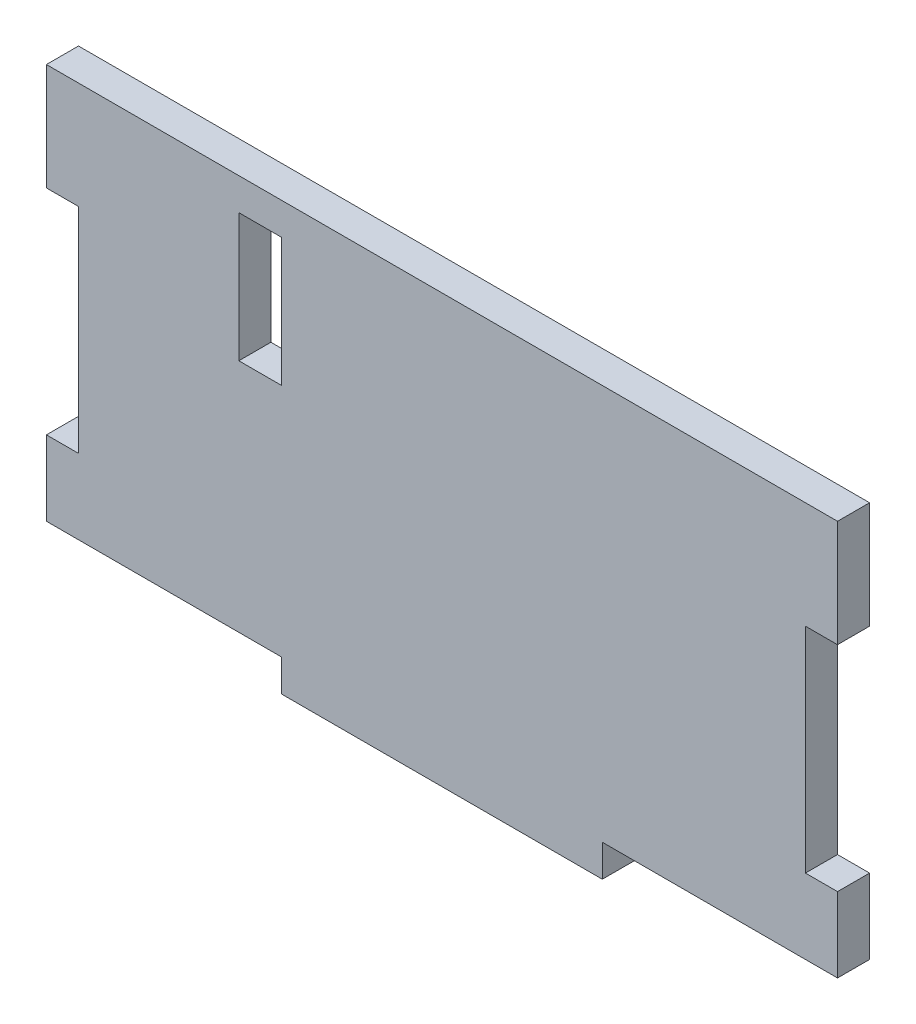
SolidWorks part; units mm, degrees
ref_plane "Plano frontal" through (0, 0, 0) normal (0, 0, 1) x (1, 0, 0)
ref_plane "Plano superior" through (0, 0, 0) normal (0, 1, 0) x (1, 0, 0)
ref_plane "Plano direito" through (0, 0, 0) normal (1, 0, 0) x (0, 0, -1)
sketch "Esboço1" plane through (0, 0, 0) normal (0, 0, 1) x (1, 0, 0)
  line L1 (-37, -20) -> (37, -20)
  line L2 (-37, -20) -> (-37, 20)
  line L3 (-37, 20) -> (37, 20)
  line L4 (37, -20) -> (37, 20)
  line L5 (-37, -20) -> (37, 20) construction
  line L6 (-37, 20) -> (37, -20) construction
  point P0 (0, 0)
  dimension "D1" = 74
  dimension "D2" = 40
extrude "Ressalto-extrusão1" add sketch "Esboço1" along normal blind 3
sketch "Esboço2" plane through (0, 0, 3) normal (0, 0, 1) x (1, 0, 0)
  line L0 (-37, -20) -> (37, -20) construction
  line L1 (-15, -20) -> (15, -20) construction
  line L2 (-15, -20) -> (-15, -17) construction
  line L3 (-15, -17) -> (15, -17) construction
  line L4 (15, -20) -> (15, -17) construction
  line L5 (-37, 20) -> (-37, -20) construction
  line L6 (-15, -20) -> (-37, -20)
  line L7 (-15, -20) -> (-15, -17)
  line L8 (-15, -17) -> (-37, -17)
  line L9 (-37, -20) -> (-37, -17)
  line L10 (0, 29.2787) -> (0, -21.4217) construction
  line L11 (15, -17) -> (37, -17)
  line L12 (15, -17) -> (15, -20)
  line L13 (15, -20) -> (37, -20)
  line L14 (37, -17) -> (37, -20)
  line L15 (-37, 10) -> (-34, 10)
  line L16 (-37, 10) -> (-37, -10)
  line L17 (-37, -10) -> (-34, -10)
  line L18 (-34, 10) -> (-34, -10)
  line L19 (34, 10) -> (34, -10)
  line L20 (37, -10) -> (34, -10)
  line L21 (37, 10) -> (37, -10)
  line L22 (37, 10) -> (34, 10)
  point P6 (0, -17)
  point P16 (-34, 0)
  dimension "D1" = 30
  dimension "D2" = 3
  dimension "D3" = 20
extrude "Corte-extrusão1" cut sketch "Esboço2" against normal blind 3
sketch "Esboço3" plane through (0, 0, 3) normal (0, 0, 1) x (1, 0, 0)
  line L0 (37, 20) -> (-37, 20) construction
  line L1 (-19, 17) -> (19, 17) construction
  line L2 (-19, 17) -> (-19, 5) construction
  line L3 (-19, 5) -> (19, 5) construction
  line L4 (19, 17) -> (19, 5) construction
  line L5 (-19, 17) -> (-15, 17)
  line L6 (-19, 17) -> (-19, 5)
  line L7 (-19, 5) -> (-15, 5)
  line L8 (-15, 17) -> (-15, 5)
  point P9 (0, 5)
  dimension "D1" = 38
  dimension "D2" = 12
  dimension "D3" = 4
  dimension "D4" = 3
extrude "Corte-extrusão2" cut sketch "Esboço3" against normal blind 10
